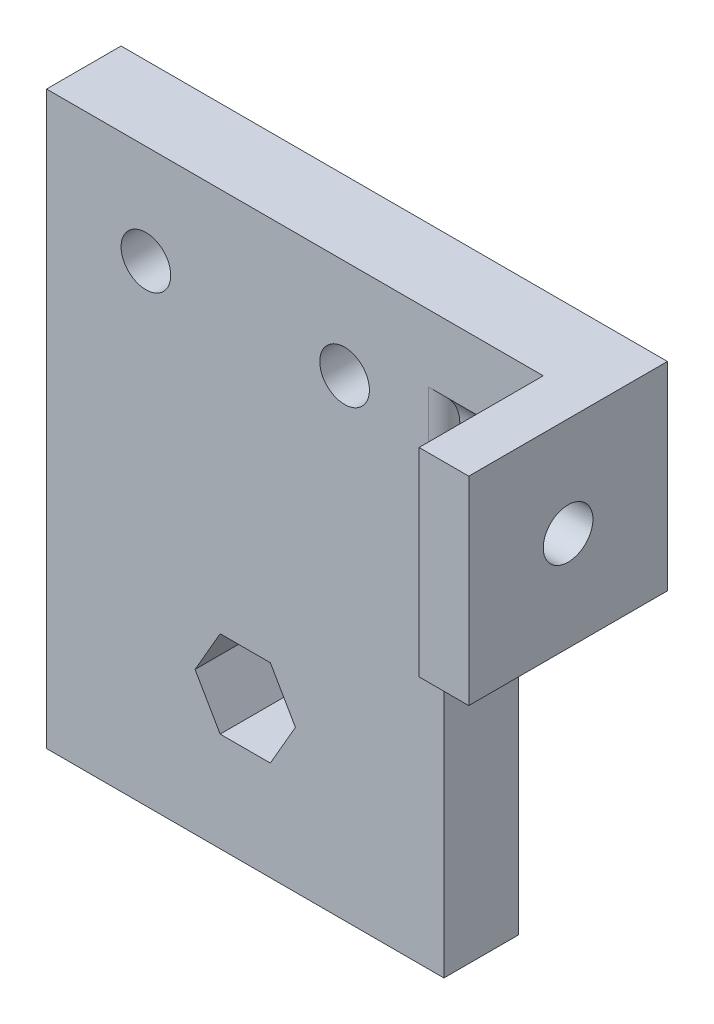
SolidWorks part; units mm, degrees
material "ABS"
ref_plane "Front Plane" through (0, 0, 0) normal (0, 0, 1) x (1, 0, 0)
ref_plane "Top Plane" through (0, 0, 0) normal (0, 1, 0) x (1, 0, 0)
ref_plane "Right Plane" through (0, 0, 0) normal (1, 0, 0) x (0, 0, -1)
sketch "Sketch2" plane through (0, 0, 0) normal (0, 0, 1) x (1, 0, 0)
  line L0 (25.4, 73.025) -> (25.4, -36.5125) construction
  line L1 (0, 0) -> (50.8, 0)
  line L2 (0, 0) -> (0, 73.025)
  line L3 (0, 73.025) -> (50.8, 73.025)
  line L4 (50.8, 0) -> (50.8, 47.625)
  line L6 (31.8158, 18.2562) -> (28.6079, 23.8125)
  line L7 (28.6079, 23.8125) -> (22.1921, 23.8125)
  line L8 (22.1921, 23.8125) -> (18.9842, 18.2562)
  line L9 (18.9842, 18.2562) -> (22.1921, 12.7)
  line L10 (22.1921, 12.7) -> (28.6079, 12.7)
  line L11 (28.6079, 12.7) -> (31.8158, 18.2562)
  line L12 (50.8, 73.025) -> (63.5, 73.025)
  line L14 (50.8, 47.625) -> (63.5, 47.625)
  line L15 (63.5, 73.025) -> (63.5, 47.625)
  circle A0 centre (12.7, 60.325) radius 3.175
  circle A1 centre (38.1, 60.325) radius 3.175
  circle A2 centre (25.4, 18.2562) radius 5.5562 construction
  dimension "D3" = 6.35
  dimension "D1" = 50.8
  dimension "D2" = 73.025
  dimension "D4" = 12.7
  dimension "D5" = 12.7
  dimension "D6" = 18.2562
  dimension "D7" = 25.4
  dimension "D8" = 12.7
extrude "Extrude1" add sketch "Sketch2" along normal blind 9.525
sketch "Sketch3" plane through (50.8, 0, 0) normal (1, 0, 0) x (0, 0, -1)
  line L0 (0, 0) -> (0, 47.625) construction
  line L5 (-25.4, 73.025) -> (0, 73.025)
  line L6 (-25.4, 73.025) -> (-25.4, 47.625)
  line L7 (-25.4, 47.625) -> (0, 47.625)
  line L8 (0, 73.025) -> (0, 47.625)
  circle A0 centre (-12.7, 60.325) radius 3.175
  dimension "D2" = 6.35
  dimension "D1" = 25.4
  dimension "D3" = 25.4
  dimension "D4" = 12.7
  dimension "D5" = 12.7
  dimension "D6" = 0
extrude "Extrude2" add sketch "Sketch3" along normal blind 6.35 from offset 12.7
sketch "Sketch4" plane through (63.5, 0, 0) normal (-1, 0, 0) x (0, 0, 1)
  circle A0 centre (12.7, 60.325) radius 5.207
  dimension "D1" = 10.414
extrude "Extrude3" cut sketch "Sketch4" along normal blind 12.7
fillet "Fillet4" radius 2 1 edges at (50.8, 60.325, 9.525)
